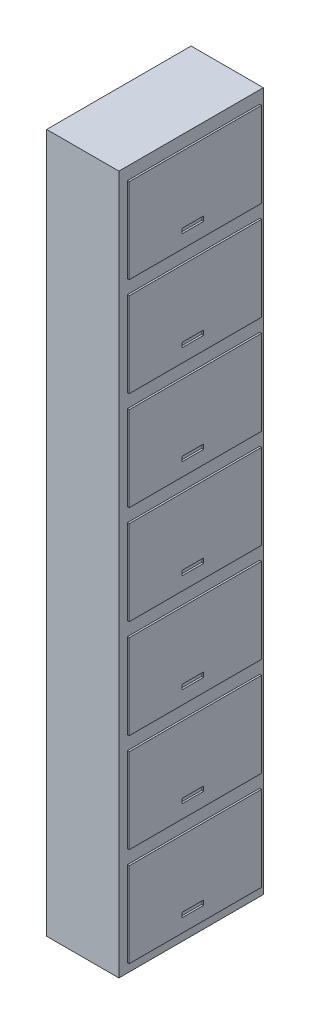
SolidWorks part; units mm, degrees
ref_plane "Front Plane" through (0, 0, 0) normal (0, 0, 1) x (1, 0, 0)
ref_plane "Top Plane" through (0, 0, 0) normal (0, 1, 0) x (1, 0, 0)
ref_plane "Right Plane" through (0, 0, 0) normal (1, 0, 0) x (0, 0, -1)
sketch "Sketch1" plane through (0, 0, 0) normal (0, 0, 1) x (1, 0, 0)
  line L0 (263.062, 4179.9863) -> (-136.938, 4179.9863)
  line L1 (-136.938, 4179.9863) -> (-136.938, 309.9863)
  line L2 (-136.938, 309.9863) -> (263.062, 309.9863)
  line L5 (263.062, 309.9863) -> (263.062, 4179.9863)
  dimension "D1" = 400
  dimension "D2" = 3870
extrude "Boss-Extrude1" add sketch "Sketch1" along normal blind 800
sketch "Sketch3" plane through (263.062, 0, 0) normal (1, 0, 0) x (0, 0, -1)
  line L1 (-752.8351, 359.9863) -> (-20, 359.9863)
  line L2 (-752.8351, 359.9863) -> (-752.8351, 829.9863)
  line L3 (-752.8351, 829.9863) -> (-20, 829.9863)
  line L4 (-20, 359.9863) -> (-20, 829.9863)
  line L5 (-800, 309.9863) -> (0, 309.9863) construction
  line L6 (-752.8351, 906.7588) -> (-20, 906.7588)
  line L7 (-461.6648, -2274.1108) -> (-340.5919, -2274.1108)
  line L8 (-461.6648, -2274.1108) -> (-461.6648, -2299.9132)
  line L9 (-461.6648, -2299.9132) -> (-340.5919, -2299.9132)
  line L10 (-340.5919, -2274.1108) -> (-340.5919, -2299.9132)
  line L11 (-752.8351, 906.7588) -> (-752.8351, 1376.7588)
  line L12 (-752.8351, 1376.7588) -> (-20, 1376.7588)
  line L13 (-20, 906.7588) -> (-20, 1376.7588)
  line L14 (-461.6648, -1727.3383) -> (-340.5919, -1727.3383)
  line L15 (-461.6648, -1753.1407) -> (-340.5919, -1753.1407)
  line L16 (-461.6648, -1727.3383) -> (-461.6648, -1753.1407)
  line L17 (-340.5919, -1727.3383) -> (-340.5919, -1753.1407)
  line L18 (-752.8351, 1453.5313) -> (-20, 1453.5313)
  line L19 (-752.8351, 1453.5313) -> (-752.8351, 1923.5313)
  line L20 (-752.8351, 1923.5313) -> (-20, 1923.5313)
  line L21 (-20, 1453.5313) -> (-20, 1923.5313)
  line L26 (-752.8351, 2000.3038) -> (-20, 2000.3038)
  line L27 (-752.8351, 2000.3038) -> (-752.8351, 2470.3038)
  line L28 (-752.8351, 2470.3038) -> (-20, 2470.3038)
  line L29 (-20, 2000.3038) -> (-20, 2470.3038)
  line L36 (-752.8351, 2547.0763) -> (-20, 2547.0763)
  line L37 (-752.8351, 2547.0763) -> (-752.8351, 3017.0763)
  line L38 (-752.8351, 3017.0763) -> (-20, 3017.0763)
  line L39 (-20, 2547.0763) -> (-20, 3017.0763)
  line L44 (-752.8351, 3093.8488) -> (-20, 3093.8488)
  line L45 (-752.8351, 3093.8488) -> (-752.8351, 3563.8488)
  line L46 (-752.8351, 3563.8488) -> (-20, 3563.8488)
  line L47 (-20, 3093.8488) -> (-20, 3563.8488)
  line L48 (-461.6648, 459.7517) -> (-340.5919, 459.7517)
  line L49 (-461.6648, 433.9492) -> (-340.5919, 433.9492)
  line L50 (-461.6648, 459.7517) -> (-461.6648, 433.9492)
  line L51 (-340.5919, 459.7517) -> (-340.5919, 433.9492)
  line L52 (-752.8351, 3640.6212) -> (-20, 3640.6212)
  line L53 (-752.8351, 3640.6212) -> (-752.8351, 4110.6212)
  line L54 (-752.8351, 4110.6212) -> (-20, 4110.6212)
  line L55 (-20, 3640.6212) -> (-20, 4110.6212)
  line L56 (-461.6648, 1006.5241) -> (-340.5919, 1006.5241)
  line L57 (-461.6648, 980.7217) -> (-340.5919, 980.7217)
  line L58 (-461.6648, 1006.5241) -> (-461.6648, 980.7217)
  line L59 (-340.5919, 1006.5241) -> (-340.5919, 980.7217)
  line L64 (-461.6648, 1553.2966) -> (-340.5919, 1553.2966)
  line L65 (-461.6648, 1527.4942) -> (-340.5919, 1527.4942)
  line L66 (-461.6648, 1553.2966) -> (-461.6648, 1527.4942)
  line L67 (-340.5919, 1553.2966) -> (-340.5919, 1527.4942)
  line L72 (-461.6648, 2100.0691) -> (-340.5919, 2100.0691)
  line L73 (-461.6648, 2074.2667) -> (-340.5919, 2074.2667)
  line L74 (-461.6648, 2100.0691) -> (-461.6648, 2074.2667)
  line L75 (-340.5919, 2100.0691) -> (-340.5919, 2074.2667)
  line L80 (-461.6648, 2646.8416) -> (-340.5919, 2646.8416)
  line L81 (-461.6648, 2621.0392) -> (-340.5919, 2621.0392)
  line L82 (-461.6648, 2646.8416) -> (-461.6648, 2621.0392)
  line L83 (-340.5919, 2646.8416) -> (-340.5919, 2621.0392)
  line L88 (-461.6648, 3193.6141) -> (-340.5919, 3193.6141)
  line L89 (-461.6648, 3167.8117) -> (-340.5919, 3167.8117)
  line L90 (-461.6648, 3193.6141) -> (-461.6648, 3167.8117)
  line L91 (-340.5919, 3193.6141) -> (-340.5919, 3167.8117)
  line L96 (-461.6648, 3740.3866) -> (-340.5919, 3740.3866)
  line L97 (-461.6648, 3714.5842) -> (-340.5919, 3714.5842)
  line L98 (-461.6648, 3740.3866) -> (-461.6648, 3714.5842)
  line L99 (-340.5919, 3740.3866) -> (-340.5919, 3714.5842)
  line L116 (-752.8351, 4734.1662) -> (-752.8351, 5204.1662) [skipped]
  line L117 (-752.8351, 5204.1662) -> (-20, 5204.1662) [skipped]
  line L118 (-20, 4734.1662) -> (-20, 5204.1662) [skipped]
  line L119 (-752.8351, 5280.9387) -> (-20, 5280.9387) [skipped]
  line L120 (-752.8351, 5280.9387) -> (-752.8351, 5750.9387) [skipped]
  line L121 (-752.8351, 5750.9387) -> (-20, 5750.9387) [skipped]
  line L122 (-20, 5280.9387) -> (-20, 5750.9387) [skipped]
  line L123 (-752.8351, 5827.7112) -> (-20, 5827.7112) [skipped]
  line L124 (-752.8351, 5827.7112) -> (-752.8351, 6297.7112) [skipped]
  line L125 (-752.8351, 6297.7112) -> (-20, 6297.7112) [skipped]
  line L126 (-20, 5827.7112) -> (-20, 6297.7112) [skipped]
  line L127 (-752.8351, 6374.4837) -> (-20, 6374.4837) [skipped]
  line L128 (-752.8351, 6374.4837) -> (-752.8351, 6844.4837) [skipped]
  line L129 (-752.8351, 6844.4837) -> (-20, 6844.4837) [skipped]
  line L130 (-20, 6374.4837) -> (-20, 6844.4837) [skipped]
  line L131 (-752.8351, 6921.2562) -> (-20, 6921.2562) [skipped]
  line L132 (-752.8351, 6921.2562) -> (-752.8351, 7391.2562) [skipped]
  line L133 (-752.8351, 7391.2562) -> (-20, 7391.2562) [skipped]
  line L134 (-20, 6921.2562) -> (-20, 7391.2562) [skipped]
  line L135 (-752.8351, 7468.0286) -> (-20, 7468.0286) [skipped]
  line L136 (-752.8351, 7468.0286) -> (-752.8351, 7938.0286) [skipped]
  line L137 (-752.8351, 7938.0286) -> (-20, 7938.0286) [skipped]
  line L138 (-20, 7468.0286) -> (-20, 7938.0286) [skipped]
  line L139 (-752.8351, 4187.3937) -> (-752.8351, 4657.3937) [skipped]
  line L140 (-752.8351, 4657.3937) -> (-20, 4657.3937) [skipped]
  line L141 (-20, 4187.3937) -> (-20, 4657.3937) [skipped]
  line L142 (-752.8351, 4734.1662) -> (-20, 4734.1662) [skipped]
  line L143 (-461.6648, 4833.9315) -> (-340.5919, 4833.9315) [skipped]
  line L144 (-461.6648, 4808.1291) -> (-340.5919, 4808.1291) [skipped]
  line L145 (-461.6648, 4833.9315) -> (-461.6648, 4808.1291) [skipped]
  line L146 (-340.5919, 4833.9315) -> (-340.5919, 4808.1291) [skipped]
  line L147 (-752.8351, 4187.3937) -> (-20, 4187.3937) [skipped]
  line L148 (-461.6648, 4287.1591) -> (-340.5919, 4287.1591) [skipped]
  line L149 (-461.6648, 4261.3567) -> (-340.5919, 4261.3567) [skipped]
  line L150 (-461.6648, 4287.1591) -> (-461.6648, 4261.3567) [skipped]
  line L151 (-340.5919, 4287.1591) -> (-340.5919, 4261.3567) [skipped]
  line L152 (-461.6648, -1180.5658) -> (-340.5919, -1180.5658) [skipped]
  line L153 (-461.6648, -1206.3682) -> (-340.5919, -1206.3682) [skipped]
  line L154 (-461.6648, -1180.5658) -> (-461.6648, -1206.3682) [skipped]
  line L155 (-340.5919, -1180.5658) -> (-340.5919, -1206.3682) [skipped]
  line L156 (-461.6648, -633.7933) -> (-340.5919, -633.7933) [skipped]
  line L157 (-461.6648, -659.5957) -> (-340.5919, -659.5957) [skipped]
  line L158 (-461.6648, -633.7933) -> (-461.6648, -659.5957) [skipped]
  line L159 (-340.5919, -633.7933) -> (-340.5919, -659.5957) [skipped]
  line L160 (-461.6648, -87.0208) -> (-340.5919, -87.0208) [skipped]
  line L161 (-461.6648, -112.8232) -> (-340.5919, -112.8232) [skipped]
  line L162 (-461.6648, -87.0208) -> (-461.6648, -112.8232) [skipped]
  line L163 (-340.5919, -87.0208) -> (-340.5919, -112.8232) [skipped]
  dimension "D1" = 470
  dimension "D3" = 50
  dimension "D4" = 14
extrude "Boss-Extrude3" add sketch "Sketch3" along normal blind 10
